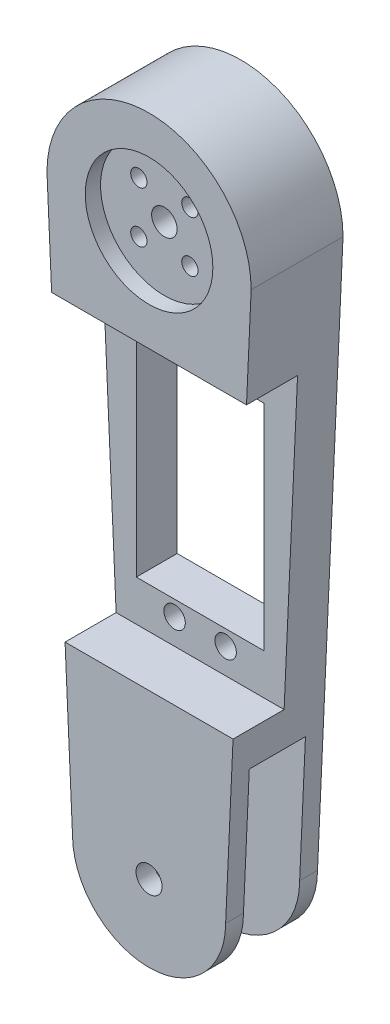
SolidWorks part; units mm, degrees
ref_plane "Front Plane" through (0, 0, 0) normal (0, 0, 1) x (1, 0, 0)
ref_plane "Top Plane" through (0, 0, 0) normal (0, 1, 0) x (1, 0, 0)
ref_plane "Right Plane" through (0, 0, 0) normal (1, 0, 0) x (0, 0, -1)
sketch "Sketch1" plane through (0, 0, 0) normal (0, 0, 1) x (1, 0, 0)
  line L0 (-20, 110) -> (-15, 0)
  line L5 (20, 110) -> (15, 0)
  line L6 (-45.614, 0) -> (42.7568, 0) construction
  circle A0 centre (0, 0) radius 15
  circle A1 centre (0, 110) radius 20
  circle A2 centre (0, 0) radius 2.55
  dimension "D1" = 30
  dimension "4" = 40
  dimension "D7" = 5.1
  dimension "D4" = 110
  dimension "D5" = 0
extrude "Boss-Extrude1" add sketch "Sketch1" along normal blind 18
sketch "Sketch2" plane through (0, 0, 18) normal (0, 0, 1) x (1, 0, 0)
  circle A0 centre (0, 110) radius 12.5
  dimension "D1" = 25
extrude "Cut-Extrude1" cut sketch "Sketch2" against normal blind 3
sketch "Sketch3" plane through (0, 0, 0) normal (0, 0, -1) x (-1, 0, 0)
  circle A0 centre (0, 110) radius 12.5
  dimension "D1" = 25
extrude "Cut-Extrude2" cut sketch "Sketch3" against normal blind 3
sketch "Sketch4" plane through (0, 0, 15) normal (0, 0, 1) x (1, 0, 0)
  line L0 (-12.5, 110) -> (12.5, 110) construction
  line L1 (0, 97.5) -> (0, 122.5) construction
  circle A0 centre (0, 110) radius 2.5
  circle A1 centre (0, 110) radius 12.5 construction
  circle A2 centre (0, 110) radius 12.5 construction
  circle A3 centre (-5, 115) radius 1.6
  circle A4 centre (-5, 105) radius 1.6
  circle A5 centre (5, 105) radius 1.6
  circle A6 centre (5, 115) radius 1.6
  dimension "D1" = 5
  dimension "D2" = 3.2
  dimension "D3" = 5
  dimension "D4" = 5
extrude "Cut-Extrude3" cut sketch "Sketch4" against normal through all
sketch "Sketch5" plane through (0, 0, 0) normal (1, 0, 0) x (0, 0, -1)
  line L1 (-14.5, -15) -> (-3.5, -15)
  line L2 (-14.5, -15) -> (-14.5, 25)
  line L3 (-14.5, 25) -> (-3.5, 25)
  line L4 (-3.5, -15) -> (-3.5, 25)
  line L6 (-18, -15) -> (0, -15) construction
  line L7 (0, 110) -> (0, 0) construction
  line L8 (-18, 110) -> (-18, 0) construction
  dimension "D1" = 40
  dimension "D2" = 3.5
  dimension "D3" = 3.5
  dimension "D4" = 0
extrude "Cut-Extrude4" cut sketch "Sketch5" against normal through all both and the other way through all
sketch "Sketch7" plane through (0, 0, 18) normal (0, 0, 1) x (1, 0, 0)
  line L1 (-20, 90) -> (20, 90)
  line L2 (-20, 90) -> (-20, 32)
  line L3 (-20, 32) -> (20, 32)
  line L4 (20, 90) -> (20, 32)
  arc A0 (20, 110) -> (-20, 110) centre (0, 110) ccw construction
  point P7 (0, 130)
  point P8 (0, 90)
  dimension "D1" = 58
  dimension "D2" = 40
  dimension "D3" = 40
  dimension "D4" = 0
extrude "Cut-Extrude5" cut sketch "Sketch7" against normal blind 10
sketch "Sketch8" plane through (0, 0, 8) normal (0, 0, 1) x (1, 0, 0)
  line L1 (-12.5, 82) -> (12.5, 82)
  line L2 (-12.5, 82) -> (-12.5, 40)
  line L3 (-12.5, 40) -> (12.5, 40)
  line L4 (12.5, 82) -> (12.5, 40)
  line L7 (-12.5, 61) -> (12.5, 61) construction
  circle A0 centre (-5, 85) radius 2.1
  circle A2 centre (0, 110) radius 2.5 construction
  circle A3 centre (5, 85) radius 2.1
  circle A4 centre (5, 37) radius 2.1
  circle A5 centre (-5, 37) radius 2.1
  dimension "D2" = 4.2
  dimension "D1" = 25
  dimension "D3" = 3
  dimension "D4" = 42
  dimension "D5" = 7.5
  dimension "D6" = 25
  dimension "D7" = 10
  dimension "D8" = 3
  dimension "D9" = 10
  dimension "D10" = 3
extrude "Cut-Extrude6" cut sketch "Sketch8" against normal through all
